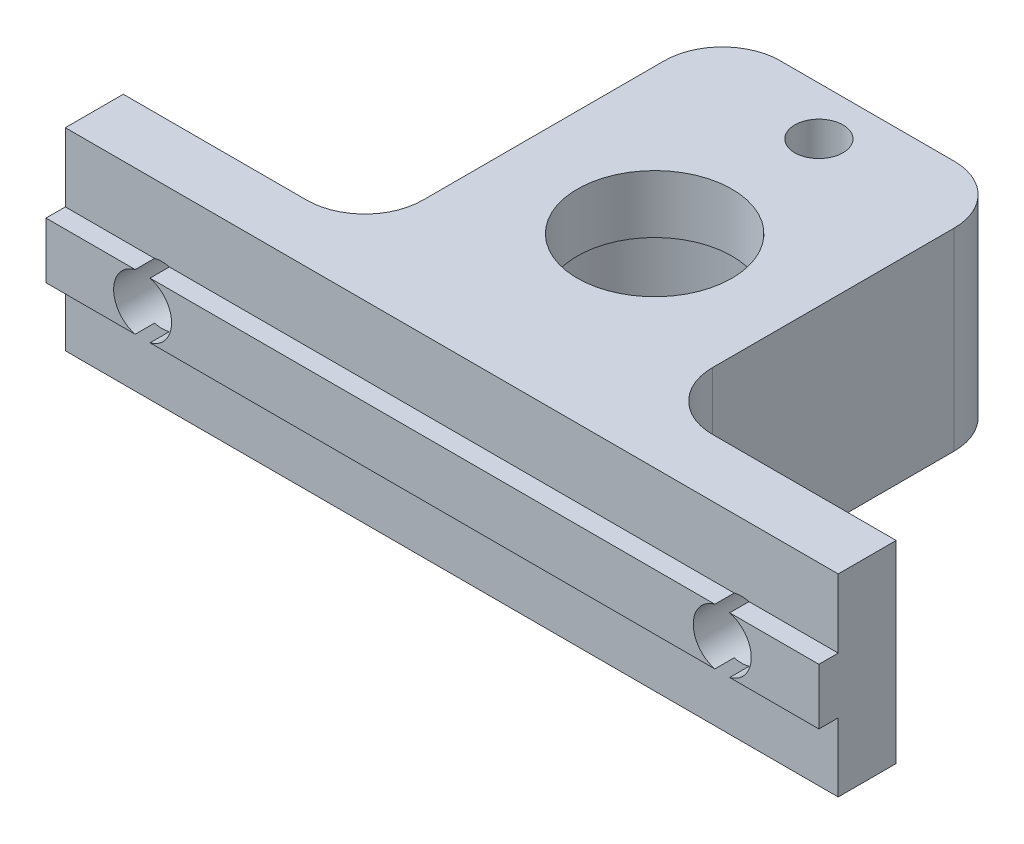
SolidWorks part; units mm, degrees
ref_plane "Front Plane" through (0, 0, 0) normal (0, 0, 1) x (1, 0, 0)
ref_plane "Top Plane" through (0, 0, 0) normal (0, 1, 0) x (1, 0, 0)
ref_plane "Right Plane" through (0, 0, 0) normal (1, 0, 0) x (0, 0, -1)
sketch "Esquisse1" plane through (0, 0, 0) normal (0, 0, 1) x (1, 0, 0)
  line L1 (-20, 0) -> (20, 0)
  line L2 (-20, 0) -> (-20, 10)
  line L3 (-20, 10) -> (20, 10)
  line L4 (20, 0) -> (20, 10)
  point P5 (0, 0)
  dimension "D1" = 40
  dimension "D2" = 10
extrude "Main" add sketch "Esquisse1" along normal blind 3
sketch "Esquisse2" plane through (0, 0, 3) normal (0, 0, 1) x (1, 0, 0)
  line L0 (20, 0) -> (20, 10) construction
  line L1 (20, 3.55) -> (-20, 3.55)
  line L2 (20, 3.55) -> (20, 6.45)
  line L3 (20, 6.45) -> (-20, 6.45)
  line L4 (-20, 3.55) -> (-20, 6.45)
  line L5 (-20, 10) -> (-20, 0) construction
  point P8 (-20, 5)
  point P9 (-20, 5)
  dimension "D1" = 2.9
extrude "MakerBeamRail" add sketch "Esquisse2" along normal blind 1
sketch "Esquisse3" plane through (0, 0, 0) normal (0, 0, -1) x (-1, 0, 0)
  line L0 (-20, 0) -> (-20, 10) construction
  circle A0 centre (-15, 5) radius 1.5
  point P5 (-20, 5)
  dimension "D1" = 3
  dimension "D2" = 5
extrude "MakerBeamHole" cut sketch "Esquisse3" against normal through all
pattern_linear "MakerBeamHoleRepeat" count 2 spacing 30 along (-1, 0, 0) of "MakerBeamHole"
sketch "Sketch3" plane through (0, 0, 0) normal (0, 1, 0) x (1, 0, 0)
  line L0 (20, 0) -> (-20, 0) construction
  line L1 (-7.5, 0) -> (7.5, 0)
  line L2 (-7.5, 0) -> (-7.5, 18.5)
  line L3 (-7.5, 18.5) -> (7.5, 18.5)
  line L4 (7.5, 0) -> (7.5, 18.5)
  point P7 (0, 18.5)
  dimension "D1" = 18.5
  dimension "D2" = 15
extrude "MagnetSupport" add sketch "Sketch3" along normal blind 10
fillet "Fillet5" radius 3 4 edges at (7.5, 5, 0) (-7.5, 5, 0) (-7.5, 5, -18.5) (7.5, 5, -18.5)
sketch "Sketch4" plane through (0, 0, 0) normal (0, -1, 0) x (1, 0, 0)
  line L0 (-14.6159, 3) -> (14.6159, 3) construction
  circle A0 centre (0, -7.5) radius 6.2
  dimension "D1" = 12.4
  dimension "D2" = 10.5
extrude "MagnetBigHole" cut sketch "Sketch4" against normal blind 7
sketch "Sketch5" plane through (0, 7, 0) normal (0, -1, 0) x (1, 0, 0)
  circle A0 centre (0, -7.5) radius 4
  circle A1 centre (0, -7.5) radius 6.2 construction
  dimension "D1" = 8
extrude "MagnetSmallHole" cut sketch "Sketch5" against normal through all
sketch "Sketch6" plane through (0, 10, 0) normal (0, 1, 0) x (1, 0, 0)
  line L0 (14.6159, -3) -> (-14.6159, -3) construction
  circle A0 centre (0, 16) radius 1.25
  dimension "D1" = 2.5
  dimension "D2" = 19
extrude "SubMagnetFixHole" cut sketch "Sketch6" against normal through all
